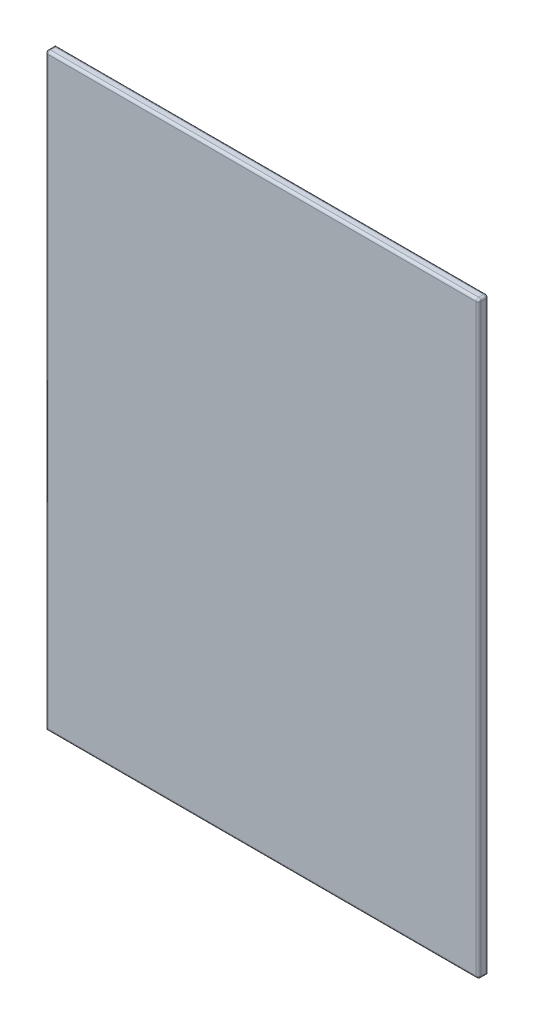
SolidWorks part; units mm, degrees
material "Acrylic (Medium-high impact)"
ref_plane "Front Plane" through (0, 0, 0) normal (0, 0, 1) x (1, 0, 0)
ref_plane "Top Plane" through (0, 0, 0) normal (0, 1, 0) x (1, 0, 0)
ref_plane "Right Plane" through (0, 0, 0) normal (1, 0, 0) x (0, 0, -1)
sketch "Sketch1" plane through (0, 0, 0) normal (0, 0, 1) x (1, 0, 0)
  line L1 (-437.5, 595) -> (437.5, 595)
  line L2 (-437.5, 595) -> (-437.5, -595)
  line L3 (-437.5, -595) -> (437.5, -595)
  line L4 (437.5, 595) -> (437.5, -595)
  line L5 (-437.5, 595) -> (437.5, -595) construction
  line L6 (-437.5, -595) -> (437.5, 595) construction
  point P0 (0, 0)
  dimension "D1" = 875
  dimension "D2" = 1190
extrude "Boss-Extrude1" add sketch "Sketch1" along normal blind 20
fillet "Fillet1" radius 5 9 edges at (437.5, 0, 0) (0, 595, 0) (437.5, 0, 20) (0, 595, 20) (-437.5, 0, 20) (0, -595, 20) (437.5, -595, 10) (-437.5, 595, 10) (437.5, 595, 10)
